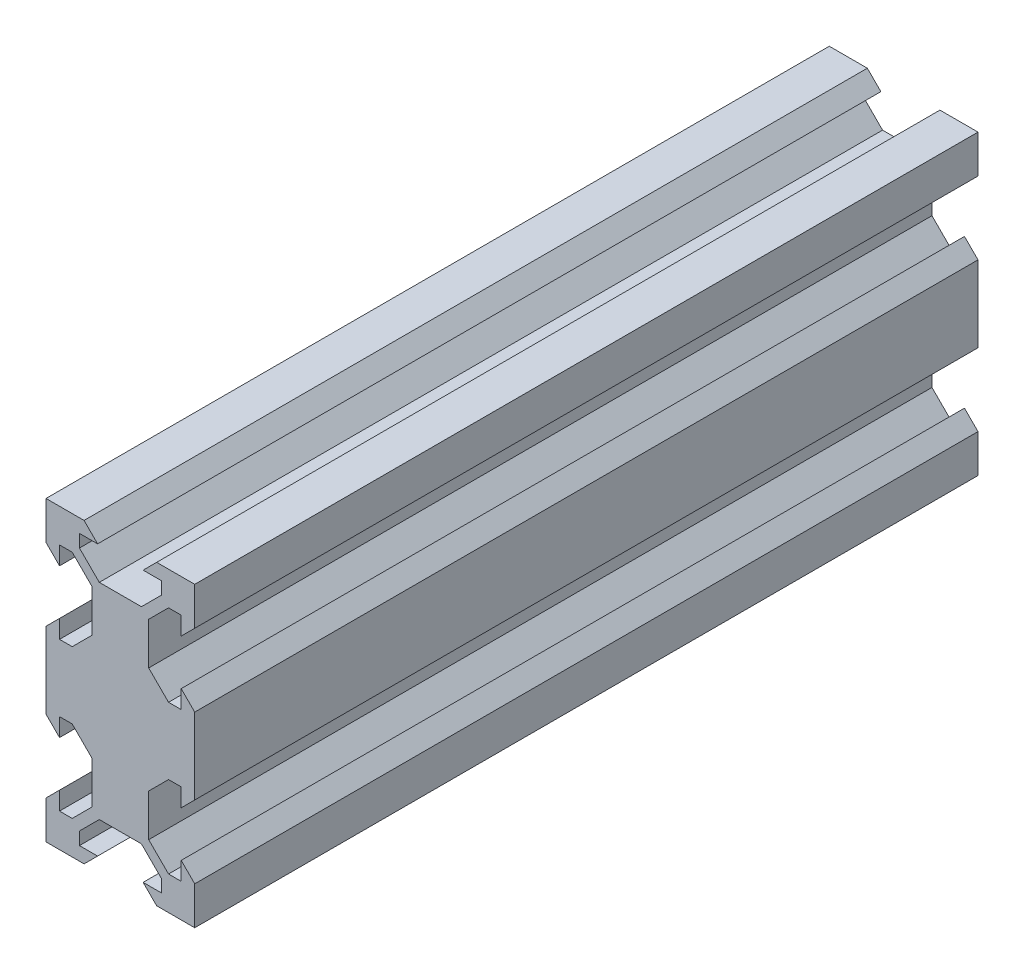
SolidWorks part; units mm, degrees
ref_plane "Front Plane" through (0, 0, 0) normal (0, 0, 1) x (1, 0, 0)
ref_plane "Top Plane" through (0, 0, 0) normal (0, 1, 0) x (1, 0, 0)
ref_plane "Right Plane" through (0, 0, 0) normal (1, 0, 0) x (0, 0, -1)
sketch "Sketch1" plane through (0, 0, 0) normal (0, 0, 1) x (1, 0, 0)
  line L1 (0, 0) -> (20, 0)
  line L2 (0, 0) -> (0, 40)
  line L3 (0, 40) -> (20, 40)
  line L4 (20, 0) -> (20, 40)
  line L5 (0, 0) -> (20, 40) construction
  line L6 (0, 40) -> (20, 0) construction
  point P4 (10, 20)
  dimension "D1" = 20
  dimension "D2" = 40
extrude "Boss-Extrude1" add sketch "Sketch1" along normal blind 105.33
sketch "Sketch2" plane through (0, 0, 105.33) normal (0, 0, 1) x (1, 0, 0)
  line L0 (5.12, 40) -> (6.94, 38.18)
  line L1 (20, 40) -> (0, 40) construction
  line L3 (13.06, 38.18) -> (14.88, 40)
  line L4 (0, 40) -> (20, 40) construction
  line L5 (20, 40) -> (10, 40) construction
  line L6 (10, 40) -> (10, 38.18) construction
  line L7 (5.12, 40) -> (14.88, 40)
  line L8 (6.94, 38.18) -> (4.5, 38.18)
  line L9 (4.5, 38.18) -> (4.5, 36.4758)
  line L10 (4.5, 36.4758) -> (7.1658, 33.81)
  line L11 (7.1658, 33.81) -> (12.8342, 33.81)
  line L12 (12.8342, 33.81) -> (15.5, 36.4758)
  line L13 (15.5, 36.4758) -> (15.5, 38.18)
  line L14 (15.5, 38.18) -> (13.06, 38.18)
  line L15 (20, 40) -> (0, 20) construction
  line L16 (0, 40) -> (0, 0) construction
  line L17 (20, 30) -> (18.18, 30) construction
  line L18 (18.18, 35.5) -> (18.18, 33.06)
  line L19 (16.4758, 35.5) -> (18.18, 35.5)
  line L20 (13.81, 32.8342) -> (16.4758, 35.5)
  line L21 (13.81, 27.1658) -> (13.81, 32.8342)
  line L22 (16.4758, 24.5) -> (13.81, 27.1658)
  line L23 (18.18, 24.5) -> (16.4758, 24.5)
  line L24 (18.18, 26.94) -> (18.18, 24.5)
  line L25 (20, 25.12) -> (20, 34.88)
  line L26 (18.18, 33.06) -> (20, 34.88)
  line L28 (20, 25.12) -> (18.18, 26.94)
  line L29 (0, 20) -> (20, 20) construction
  line L30 (20, 0) -> (20, 40) construction
  line L31 (20, 10) -> (18.18, 10) construction
  line L32 (10, 0) -> (10, 1.82) construction
  line L33 (20, 0) -> (10, 0) construction
  line L34 (20, 14.88) -> (18.18, 13.06)
  line L36 (18.18, 6.94) -> (20, 5.12)
  line L37 (20, 14.88) -> (20, 5.12)
  line L38 (18.18, 13.06) -> (18.18, 15.5)
  line L39 (18.18, 15.5) -> (16.4758, 15.5)
  line L40 (16.4758, 15.5) -> (13.81, 12.8342)
  line L41 (13.81, 12.8342) -> (13.81, 7.1658)
  line L42 (13.81, 7.1658) -> (16.4758, 4.5)
  line L43 (16.4758, 4.5) -> (18.18, 4.5)
  line L44 (18.18, 4.5) -> (18.18, 6.94)
  line L45 (15.5, 1.82) -> (13.06, 1.82)
  line L46 (15.5, 3.5242) -> (15.5, 1.82)
  line L47 (12.8342, 6.19) -> (15.5, 3.5242)
  line L48 (7.1658, 6.19) -> (12.8342, 6.19)
  line L49 (4.5, 3.5242) -> (7.1658, 6.19)
  line L50 (4.5, 1.82) -> (4.5, 3.5242)
  line L51 (6.94, 1.82) -> (4.5, 1.82)
  line L52 (5.12, 0) -> (14.88, 0)
  line L53 (13.06, 1.82) -> (14.88, 0)
  line L55 (5.12, 0) -> (6.94, 1.82)
  line L56 (10, 40) -> (10, 0) construction
  line L57 (0, 10) -> (1.82, 10) construction
  line L58 (0, 30) -> (1.82, 30) construction
  line L59 (1.82, 4.5) -> (1.82, 6.94)
  line L60 (3.5242, 4.5) -> (1.82, 4.5)
  line L61 (6.19, 7.1658) -> (3.5242, 4.5)
  line L62 (6.19, 12.8342) -> (6.19, 7.1658)
  line L63 (3.5242, 15.5) -> (6.19, 12.8342)
  line L64 (1.82, 15.5) -> (3.5242, 15.5)
  line L65 (1.82, 13.06) -> (1.82, 15.5)
  line L66 (0, 14.88) -> (0, 5.12)
  line L67 (1.82, 6.94) -> (0, 5.12)
  line L69 (0, 14.88) -> (1.82, 13.06)
  line L70 (0, 25.12) -> (1.82, 26.94)
  line L72 (1.82, 33.06) -> (0, 34.88)
  line L73 (0, 25.12) -> (0, 34.88)
  line L74 (1.82, 26.94) -> (1.82, 24.5)
  line L75 (1.82, 24.5) -> (3.5242, 24.5)
  line L76 (3.5242, 24.5) -> (6.19, 27.1658)
  line L77 (6.19, 27.1658) -> (6.19, 32.8342)
  line L78 (6.19, 32.8342) -> (3.5242, 35.5)
  line L79 (3.5242, 35.5) -> (1.82, 35.5)
  line L80 (1.82, 35.5) -> (1.82, 33.06)
  dimension "D1" = 90
  dimension "D3" = 6.12
  dimension "D5" = 11
  dimension "D6" = 6.19
  dimension "D7" = 1.38
extrude "Cut-Extrude1" cut sketch "Sketch2" against normal through all
